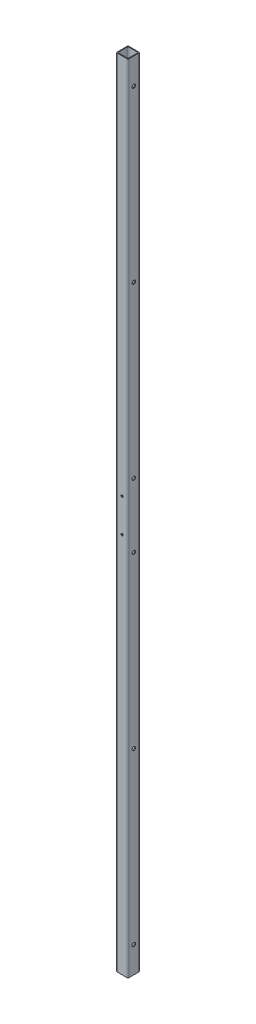
SolidWorks part; units mm, degrees
ref_plane "Front Plane" through (0, 0, 0) normal (0, 0, 1) x (1, 0, 0)
ref_plane "Top Plane" through (0, 0, 0) normal (0, 1, 0) x (1, 0, 0)
ref_plane "Right Plane" through (0, 0, 0) normal (1, 0, 0) x (0, 0, -1)
sketch "Sketch1" plane through (0, 0, 0) normal (0, 1, 0) x (1, 0, 0)
  line L0 (8.382, -8.382) -> (8.382, 8.382)
  line L1 (-9.652, -9.652) -> (9.652, -9.652)
  line L2 (-9.652, -9.652) -> (-9.652, 9.652)
  line L3 (-9.652, 9.652) -> (9.652, 9.652)
  line L4 (9.652, -9.652) -> (9.652, 9.652)
  line L5 (-9.652, -9.652) -> (9.652, 9.652) construction
  line L6 (-9.652, 9.652) -> (9.652, -9.652) construction
  line L7 (-8.382, 8.382) -> (8.382, 8.382)
  line L8 (-8.382, -8.382) -> (-8.382, 8.382)
  line L9 (-8.382, -8.382) -> (8.382, -8.382)
  point P0 (0, 0)
  dimension "D1" = 19.304
  dimension "D2" = 1.27
extrude "Boss-Extrude1" add sketch "Sketch1" along normal blind 1309.624
fillet "Fillet1" radius 1.27 8 edges at (-9.652, 654.812, 9.652) (-9.652, 654.812, -9.652) (9.652, 654.812, -9.652) (9.652, 654.812, 9.652) (-8.382, 654.812, -8.382) (8.382, 654.812, 8.382) (8.382, 654.812, -8.382) (-8.382, 654.812, 8.382)
hole_wizard "#1 (0.228) Diameter Hole1" positions "Sketch2" profile "Sketch3" hole size "#1" standard "ANSI Inch" end condition through all
sketch "Sketch2" plane through (9.652, 0, 0) normal (1, 0, 0) x (0, 0, -1)
  line L0 (0, 1309.624) -> (0, 0) construction
  line L1 (-8.382, 1309.624) -> (8.382, 1309.624) construction
  line L2 (8.382, 0) -> (-8.382, 0) construction
  line L4 (-8.382, 0) -> (8.382, 0) construction
  point P8 (0, 1266.444)
  point P82 (0, 987.044)
  point P83 (0, 707.644)
  point P84 (0, 43.18)
  point P107 (0, 322.58)
  point P108 (0, 601.98)
  dimension "D1" = 43.18
  dimension "D3" = 43.18
  dimension "D5" = 322.58
  dimension "D6" = 707.644
  dimension "D2" = 3
  dimension "D4" = 3
sketch "Sketch3" plane through (9.652, 601.98, 0) normal (0, 1, 0) x (0, 0, -1)
  line L0 (0, 0) -> (0, 19.304)
  line L1 (0, 19.304) -> (2.8956, 19.304)
  line L2 (2.8956, 19.304) -> (2.8956, 0)
  line L5 (2.8956, 0) -> (0, 0)
  line L11 (0, -6.35) -> (0, 107.95) construction
  dimension "Thru Hole Dia." = 5.7912
  dimension "Thru Hole Depth" = 19.304
hole_wizard "#8-32 Tapped Hole1" positions "Sketch4" profile "Sketch5" tap size "#8-32" standard "ANSI Inch" end condition through all
sketch "Sketch4" plane through (0, 0, -9.652) normal (0, 0, -1) x (-1, 0, 0)
  line L0 (-8.382, 0) -> (8.382, 1309.624) construction
  line L2 (0, 654.812) -> (-8.382, 654.812) construction
  line L3 (-8.382, 1309.624) -> (-8.382, 0) construction
  line L5 (0, 654.812) -> (0, 842.9154) construction
  line L6 (0, 654.812) -> (0, 575.682) construction
  point P19 (0, 682.244)
  point P25 (0, 627.38)
  dimension "D1" = 27.432
  dimension "D2" = 27.432
sketch "Sketch5" plane through (0, 627.38, -9.652) normal (1, 0, 0) x (0, 1, 0)
  line L0 (0, 0) -> (0, 19.304)
  line L1 (0, 19.304) -> (1.7272, 19.304)
  line L2 (1.7272, 19.304) -> (1.7272, 0)
  line L5 (1.7272, 0) -> (0, 0)
  line L11 (0, -6.35) -> (0, 107.95) construction
  dimension "Thru Tap Drill Dia." = 3.4544
  dimension "Thru Tap Drill Depth" = 19.304
cosmetic thread "Hole Thread1" parameters "D2"=4.1656
cosmetic thread "Hole Thread2" parameters "D2"=4.1656
